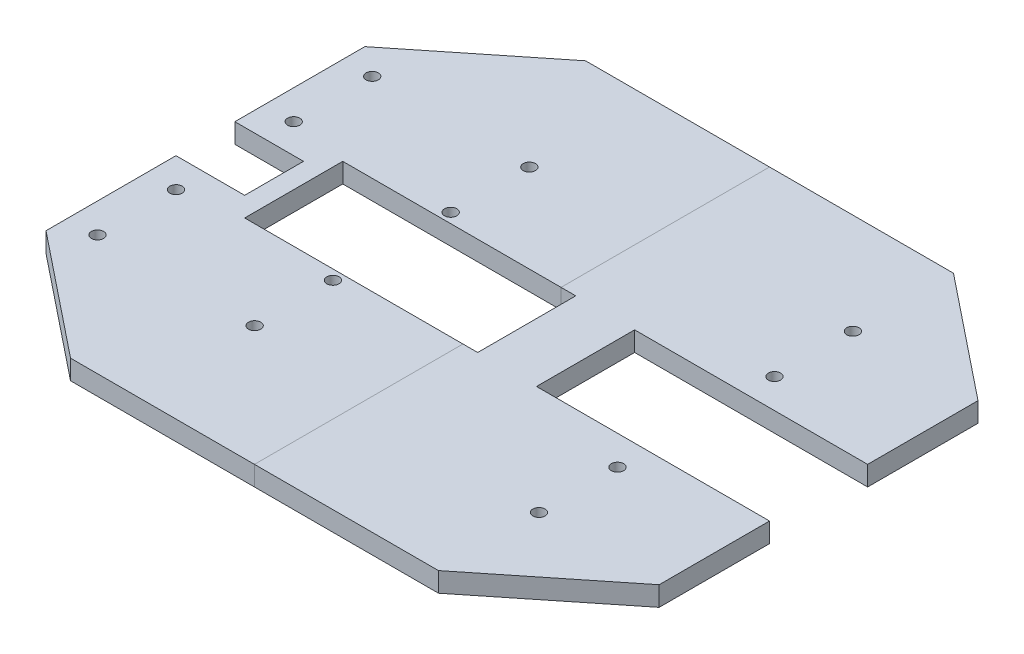
SolidWorks part; units mm, degrees
ref_plane "Front Plane" through (0, 0, 0) normal (0, 0, 1) x (1, 0, 0)
ref_plane "Top Plane" through (0, 0, 0) normal (0, 1, 0) x (1, 0, 0)
ref_plane "Right Plane" through (0, 0, 0) normal (1, 0, 0) x (0, 0, -1)
sketch "Sketch1" plane through (0, 0, 0) normal (0, 1, 0) x (1, 0, 0)
  line L1 (-107.1206, 69.9876) -> (142.8794, 69.9876)
  line L2 (-107.1206, 69.9876) -> (-107.1206, -60.0124)
  line L3 (-107.1206, -60.0124) -> (142.8794, -60.0124)
  line L4 (142.8794, 69.9876) -> (142.8794, -60.0124)
  dimension "D1" = 250
  dimension "D2" = 130
extrude "Boss-Extrude1" add sketch "Sketch1" along normal blind 8
sketch "Sketch2" plane through (0, 8, 0) normal (0, 1, 0) x (1, 0, 0)
  line L0 (142.8794, -60.0124) -> (142.8794, 69.9876) construction
  line L1 (142.8794, 24.9876) -> (47.8794, 24.9876)
  line L2 (142.8794, 24.9876) -> (142.8794, -15.0124)
  line L3 (142.8794, -15.0124) -> (47.8794, -15.0124)
  line L4 (47.8794, 24.9876) -> (47.8794, -15.0124)
  line L5 (142.8794, 69.9876) -> (-107.1206, 69.9876) construction
  dimension "D1" = 95
  dimension "D2" = 40
  dimension "D3" = 45
extrude "Cut-Extrude1" cut sketch "Sketch2" against normal up to surface (8 mm away) up to face at (17.8794, 0, -4.9876)
sketch "Sketch3" plane through (0, 8, 0) normal (0, 1, 0) x (1, 0, 0)
  line L0 (-107.1206, 69.9876) -> (-107.1206, -60.0124) construction
  line L1 (-107.1206, 16.9876) -> (-79.1206, 16.9876)
  line L2 (-107.1206, 16.9876) -> (-107.1206, -7.0124)
  line L3 (-107.1206, -7.0124) -> (-79.1206, -7.0124)
  line L4 (-79.1206, 16.9876) -> (-79.1206, -7.0124)
  line L5 (142.8794, 69.9876) -> (-107.1206, 69.9876) construction
  dimension "D1" = 28
  dimension "D2" = 24
  dimension "D3" = 53
extrude "Cut-Extrude2" cut sketch "Sketch3" against normal up to surface (8 mm away) up to face at (56.6294, 0, -4.9876)
sketch "Sketch4" plane through (0, 8, 0) normal (0, 1, 0) x (1, 0, 0)
  line L0 (-79.1206, -7.0124) -> (-79.1206, 16.9876) construction
  line L1 (-71.1206, 24.9876) -> (23.8794, 24.9876)
  line L2 (-71.1206, 24.9876) -> (-71.1206, -15.0124)
  line L3 (-71.1206, -15.0124) -> (23.8794, -15.0124)
  line L4 (23.8794, 24.9876) -> (23.8794, -15.0124)
  line L5 (142.8794, 24.9876) -> (47.8794, 24.9876) construction
  dimension "D1" = 40
  dimension "D2" = 95
  dimension "D3" = 8
extrude "Cut-Extrude3" cut sketch "Sketch4" against normal up to surface (8 mm away) up to face at (6.7127, 0, -4.9876)
sketch "Sketch5" plane through (0, 0, 0) normal (0, -1, 0) x (1, 0, 0)
  line L0 (-107.1206, 60.0124) -> (-57.1206, 100.0124)
  line L1 (-57.1206, 100.0124) -> (92.8794, 100.0124)
  line L2 (92.8794, 100.0124) -> (142.8794, 60.0124)
  line L3 (-107.1206, -69.9876) -> (-57.1206, -109.9876)
  line L4 (-57.1206, -109.9876) -> (92.8794, -109.9876)
  line L5 (92.8794, -109.9876) -> (142.8794, -69.9876)
  line L6 (142.8794, -69.9876) -> (-107.1206, -69.9876) construction
  line L7 (-107.1206, 60.0124) -> (142.8794, 60.0124) construction
  line L8 (-107.1206, 60.0124) -> (142.8794, 60.0124)
  line L9 (-107.1206, -69.9876) -> (142.8794, -69.9876)
  dimension "D1" = 40
  dimension "D2" = 40
  dimension "D3" = 50
  dimension "D4" = 50
  dimension "D5" = 50
  dimension "D6" = 50
extrude "Boss-Extrude2" add sketch "Sketch5" against normal up to surface (8 mm away) up to face at (-23.6206, 8, -4.9876)
sketch "Sketch6" plane through (0, 8, 0) normal (0, 1, 0) x (1, 0, 0)
  line L0 (47.8794, -15.0124) -> (142.8794, -15.0124) construction
  line L1 (142.8794, -60.0124) -> (142.8794, -15.0124) construction
  circle A0 centre (92.8794, -27.0124) radius 2.5
  circle A1 centre (92.8794, -59.0124) radius 2.5
  dimension "D1" = 5
  dimension "D4" = 5
  dimension "D2" = 12
  dimension "D3" = 50
  dimension "D5" = 32
extrude "Cut-Extrude4" cut sketch "Sketch6" against normal up to surface (8 mm away) up to face at (-23.6206, 0, -4.9876)
sketch "Sketch7" plane through (0, 8, 0) normal (0, 1, 0) x (1, 0, 0)
  line L0 (-71.1206, -15.0124) -> (23.8794, -15.0124) construction
  line L1 (-107.1206, -7.0124) -> (-107.1206, -60.0124) construction
  circle A0 centre (-95.1206, -19.0124) radius 2.5
  circle A1 centre (-95.1206, -51.0124) radius 2.5
  dimension "D1" = 5
  dimension "D4" = 5
  dimension "D2" = 4
  dimension "D3" = 32
  dimension "D5" = 12
extrude "Cut-Extrude5" cut sketch "Sketch7" against normal up to surface (8 mm away) up to face at (92.8794, 0, 29.5124)
ref_plane "Reflection Plane" through (0, 0, -4.9876) normal (0, 0, 1) x (1, 0, 0)
mirror "Mirror1" about plane through (0, 0, -4.9876) normal (0, 0, 1) of "Cut-Extrude4", "Cut-Extrude5"
sketch "Sketch8" plane through (0, 8, 0) normal (0, 1, 0) x (1, 0, 0)
  circle A0 centre (-31.1206, -19.0124) radius 2.5
  circle A1 centre (-31.0515, -51.0124) radius 2.5
  circle A2 centre (-95.1206, -19.0124) radius 2.5 construction
  dimension "D1" = 5
  dimension "D2" = 5
  dimension "D3" = 64
  dimension "D4" = 32
  dimension "D5" = 0
extrude "Cut-Extrude6" cut sketch "Sketch8" against normal up to surface (8 mm away) up to face at (-95.1206, 0, -26.4876)
mirror "Mirror2" about plane through (0, 0, -4.9876) normal (0, 0, 1) of "Cut-Extrude6"
ref_plane "Plane1" through (17.8794, 0, 0) normal (-1, 0, 0) x (0, 0, 1)
split "Split1" trim tools "Plane1" bodies to split 110 resulting bodies 111 112
